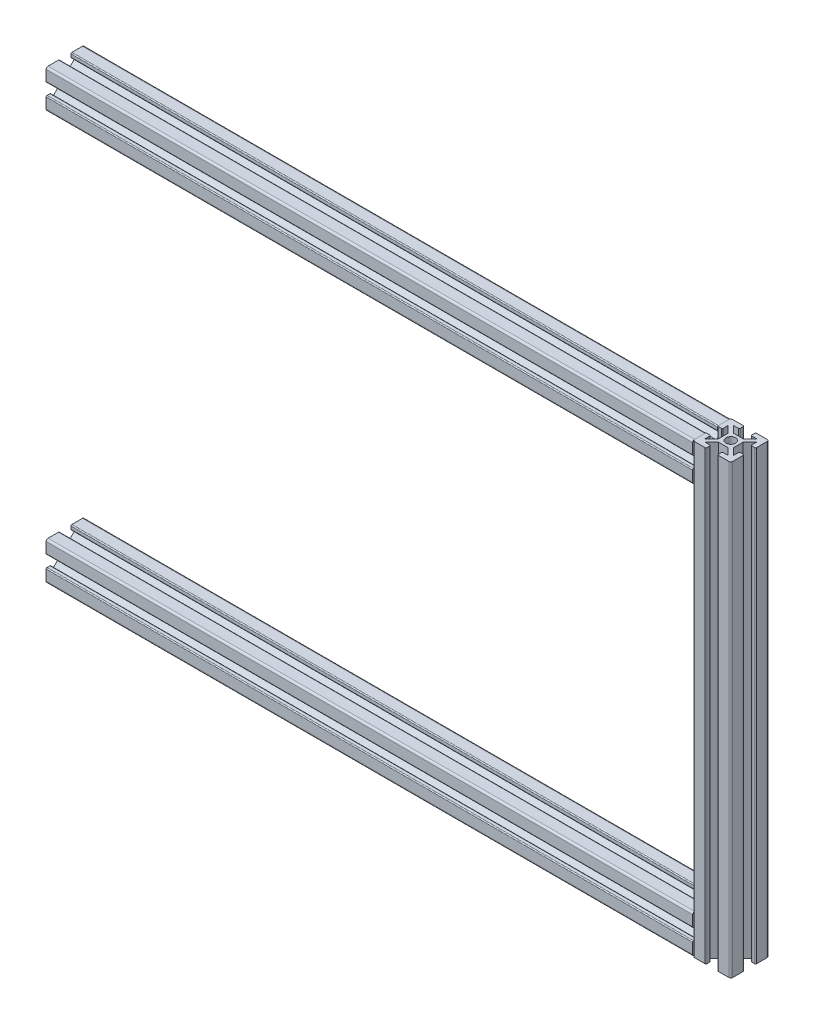
SolidWorks part; units mm, degrees
ref_plane "Front Plane" through (0, 0, 0) normal (0, 0, 1) x (1, 0, 0)
ref_plane "Top Plane" through (0, 0, 0) normal (0, 1, 0) x (1, 0, 0)
ref_plane "Right Plane" through (0, 0, 0) normal (1, 0, 0) x (0, 0, -1)
sketch "Sketch2" plane through (0, 0, 0) normal (0, 0, 1) x (1, 0, 0)
  line L0 (0, 0) -> (350, 0)
  line L1 (350, 0) -> (350, -215)
  line L2 (350, -215) -> (0, -215)
  dimension "D1" = 350
  dimension "D2" = 350
  dimension "D3" = 215
other "Aluminium prof ALUMINIUM PROF(1)"
ref_plane "Plane2" through (0, 0, 0) normal (1, 0, 0) x (0, 1, 0)
sketch "Sketch1" plane through (0, 0, 0) normal (1, 0, 0) x (0, 1, 0)
  line L0 (0, 0) -> (0, 19.0058) construction
  line L9 (0, 0) -> (23.0409, 0) construction
  line L10 (23.0409, 0) -> (23.0409, -0.0585) construction
  line L11 (23.0409, -0.0585) -> (23.0409, 0) construction
  line L13 (-2.5, 4) -> (2.5, 4)
  line L14 (2.5, 4) -> (6.0355, 7.5355)
  line L15 (6.0355, 7.5355) -> (3.5355, 7.5355)
  line L16 (3.0355, 8.0355) -> (3.0355, 9.5355)
  line L17 (3.5355, 10.0355) -> (9.0355, 10.0355)
  line L18 (10.0355, 9.0355) -> (10.0355, 3.5355)
  line L19 (9.5355, 3.0355) -> (8.0355, 3.0355)
  line L20 (7.5355, 3.5355) -> (7.5355, 6.0355)
  line L21 (7.5355, 6.0355) -> (4, 2.5)
  line L22 (4, 2.5) -> (4, -2.5)
  line L23 (-10.0355, 9.0355) -> (-10.0355, 3.5355)
  line L24 (-4, 2.5) -> (-4, -2.5)
  line L25 (-7.5355, 6.0355) -> (-4, 2.5)
  line L26 (-7.5355, 3.5355) -> (-7.5355, 6.0355)
  line L27 (-9.5355, 3.0355) -> (-8.0355, 3.0355)
  line L28 (-3.5355, 10.0355) -> (-9.0355, 10.0355)
  line L29 (-3.0355, 8.0355) -> (-3.0355, 9.5355)
  line L30 (-6.0355, 7.5355) -> (-3.5355, 7.5355)
  line L31 (-2.5, 4) -> (-6.0355, 7.5355)
  line L32 (3.5355, -10.0355) -> (9.0355, -10.0355)
  line L33 (-2.5, -4) -> (-6.0355, -7.5355)
  line L34 (-6.0355, -7.5355) -> (-3.5355, -7.5355)
  line L35 (-3.0355, -8.0355) -> (-3.0355, -9.5355)
  line L36 (-3.5355, -10.0355) -> (-9.0355, -10.0355)
  line L37 (-9.5355, -3.0355) -> (-8.0355, -3.0355)
  line L38 (-7.5355, -3.5355) -> (-7.5355, -6.0355)
  line L39 (-7.5355, -6.0355) -> (-4, -2.5)
  line L40 (-10.0355, -9.0355) -> (-10.0355, -3.5355)
  line L41 (7.5355, -6.0355) -> (4, -2.5)
  line L42 (7.5355, -3.5355) -> (7.5355, -6.0355)
  line L43 (9.5355, -3.0355) -> (8.0355, -3.0355)
  line L44 (10.0355, -9.0355) -> (10.0355, -3.5355)
  line L45 (3.0355, -8.0355) -> (3.0355, -9.5355)
  line L46 (6.0355, -7.5355) -> (3.5355, -7.5355)
  line L47 (2.5, -4) -> (6.0355, -7.5355)
  line L48 (-2.5, -4) -> (2.5, -4)
  circle A0 centre (0, 0) radius 2.5
  arc A1 (-10.0355, 9.0355) -> (-9.0355, 10.0355) centre (-9.0355, 9.0355) cw
  arc A2 (-9.0355, -10.0355) -> (-10.0355, -9.0355) centre (-9.0355, -9.0355) cw
  arc A3 (9.0355, -10.0355) -> (10.0355, -9.0355) centre (9.0355, -9.0355) ccw
  arc A4 (9.0355, 10.0355) -> (10.0355, 9.0355) centre (9.0355, 9.0355) cw
  arc A5 (-9.5355, -3.0355) -> (-10.0355, -3.5355) centre (-9.5355, -3.5355) ccw
  arc A6 (-8.0355, -3.0355) -> (-7.5355, -3.5355) centre (-8.0355, -3.5355) cw
  arc A7 (-3.5355, -7.5355) -> (-3.0355, -8.0355) centre (-3.5355, -8.0355) cw
  arc A8 (-3.0355, -9.5355) -> (-3.5355, -10.0355) centre (-3.5355, -9.5355) cw
  arc A9 (3.5355, -10.0355) -> (3.0355, -9.5355) centre (3.5355, -9.5355) cw
  arc A10 (3.0355, -8.0355) -> (3.5355, -7.5355) centre (3.5355, -8.0355) cw
  arc A11 (9.5355, -3.0355) -> (10.0355, -3.5355) centre (9.5355, -3.5355) cw
  arc A12 (7.5355, -3.5355) -> (8.0355, -3.0355) centre (8.0355, -3.5355) cw
  arc A13 (10.0355, 3.5355) -> (9.5355, 3.0355) centre (9.5355, 3.5355) cw
  arc A14 (8.0355, 3.0355) -> (7.5355, 3.5355) centre (8.0355, 3.5355) cw
  arc A15 (3.5355, 7.5355) -> (3.0355, 8.0355) centre (3.5355, 8.0355) cw
  arc A16 (3.0355, 9.5355) -> (3.5355, 10.0355) centre (3.5355, 9.5355) cw
  arc A17 (-3.5355, 10.0355) -> (-3.0355, 9.5355) centre (-3.5355, 9.5355) cw
  arc A18 (-3.0355, 8.0355) -> (-3.5355, 7.5355) centre (-3.5355, 8.0355) cw
  arc A19 (-7.5355, 3.5355) -> (-8.0355, 3.0355) centre (-8.0355, 3.5355) cw
  arc A20 (-10.0355, 3.5355) -> (-9.5355, 3.0355) centre (-9.5355, 3.5355) ccw
  point P26 (0, 4)
  point P29 (-4, 0)
  point P30 (4, 0)
  point P44 (0, -4)
  point P48 (-10.0355, 10.0355)
  point P51 (-10.0355, -10.0355)
  point P54 (10.0355, -10.0355)
  point P57 (10.0355, 10.0355)
  point P60 (-10.0355, -3.0355)
  point P63 (-7.5355, -3.0355)
  point P66 (-3.0355, -7.5355)
  point P69 (-3.0355, -10.0355)
  point P72 (3.0355, -10.0355)
  point P75 (3.0355, -7.5355)
  point P78 (10.0355, -3.0355)
  point P81 (7.5355, -3.0355)
  point P84 (10.0355, 3.0355)
  point P87 (7.5355, 3.0355)
  point P90 (3.0355, 7.5355)
  point P93 (3.0355, 10.0355)
  point P96 (-3.0355, 10.0355)
  point P99 (-3.0355, 7.5355)
  point P102 (-7.5355, 3.0355)
  point P105 (-10.0355, 3.0355)
  point P106 (0, 0)
  dimension "D5" = 4
  dimension "D12" = 1
  dimension "D13" = 0.5
  dimension "D1" = 135
  dimension "D2" = 2.5
  dimension "D3" = 4
  dimension "D4" = 2.5
  dimension "D6" = 7
  dimension "D7" = 7
  dimension "D8" = 3
  dimension "D9" = 3
  dimension "D10" = 5
  dimension "D11" = 23.0409
other "Trim/Extend1"
other "Trim/Extend2"
sketch "Sketch3" plane through (0, 4, 0) normal (0, 1, 0) x (1, 0, 0)
  line L0 (0, 0) -> (408.1297, 0) construction
  line L2 (0, 2.5) -> (0, -2.5) construction
  circle A0 centre (75, 0) radius 2.5
  circle A1 centre (175, 0) radius 2.5
  circle A2 centre (264.9645, 0) radius 2.5
  dimension "D1" = 5
  dimension "D2" = 75
  dimension "D3" = 75
  dimension "D4" = 100
  dimension "D5" = 89.9645
extrude "Cut-Extrude1" cut sketch "Sketch3" against normal blind 10
